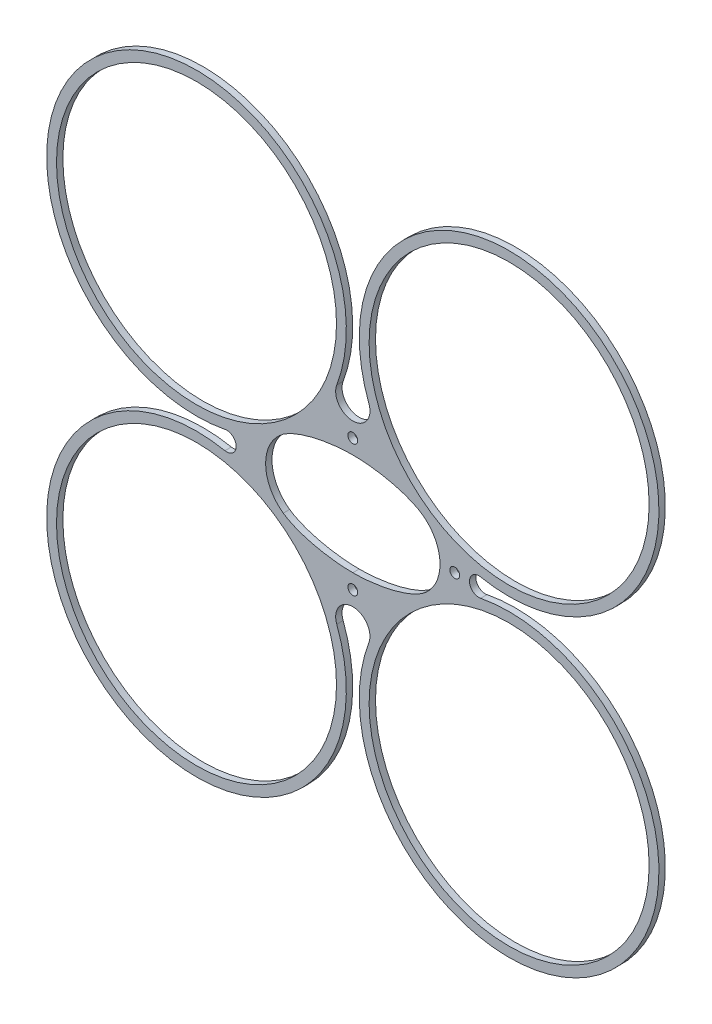
SolidWorks part; units mm, degrees
material "PC High Viscosity"
ref_plane "Front Plane" through (0, 0, 0) normal (0, 0, 1) x (1, 0, 0)
ref_plane "Top Plane" through (0, 0, 0) normal (0, 1, 0) x (1, 0, 0)
ref_plane "Right Plane" through (0, 0, 0) normal (1, 0, 0) x (0, 0, -1)
sketch "Sketch1" plane through (0, 0, 0) normal (0, 0, 1) x (1, 0, 0)
  line L0 (0, -18.1806) -> (0, 16.1577) construction
  line L1 (-47.1416, 0) -> (36.9217, 0) construction
  line L4 (-31.8198, -31.8198) -> (31.8198, 31.8198) construction
  line L6 (-31.8198, 31.8198) -> (31.8198, -31.8198) construction
  circle A0 centre (-31.8198, 31.8198) radius 28.5
  circle A2 centre (31.8198, -31.8198) radius 5.125 construction
  circle A3 centre (-31.8198, 31.8198) radius 30.5
  circle A4 centre (31.8198, 31.8198) radius 30.5
  circle A5 centre (31.8198, 31.8198) radius 28.5
  circle A6 centre (31.8198, -31.8198) radius 28.5
  circle A7 centre (31.8198, -31.8198) radius 30.5
  circle A8 centre (-31.8198, -31.8198) radius 30.5
  circle A9 centre (-31.8198, -31.8198) radius 28.5
  dimension "D1" = 57
  dimension "D2" = 2
extrude "Boss-Extrude1" add sketch "Sketch1" along normal blind 1.3
sketch "Sketch3" plane through (0, 0, 0) normal (0, 0, -1) x (-1, 0, 0)
  line L0 (-31.8198, -1.3198) -> (-31.8198, -3.3198) construction
  line L1 (-20.75, -1) -> (-20.75, -3) construction
  line L2 (-17.75, 0) -> (-23.75, 0) construction
  line L3 (-29.35, 0) -> (23.6854, 0) construction
  line L4 (0, -20.1011) -> (0, 19.2767) construction
  line L5 (0, -16.375) -> (0, -10.375) construction
  line L6 (-3, -13.375) -> (3, -13.375) construction
  line L7 (0, 0) -> (-31.8198, -31.8198) construction
  circle A0 centre (-20.75, 0) radius 1 construction
  circle A1 centre (0, 13.375) radius 1 construction
  circle A2 centre (0, -13.375) radius 1 construction
  circle A3 centre (-20.75, 0) radius 1
  circle A4 centre (0, 13.375) radius 1
  circle A5 centre (0, -13.375) radius 1
  circle A6 centre (-20.75, 0) radius 3
  circle A7 centre (-31.8198, -31.8198) radius 30.5 construction
  circle A8 centre (-31.8198, -31.8198) radius 28.5 construction
  circle A9 centre (0, -13.375) radius 3
  circle A10 centre (0, 13.375) radius 3
  arc A11 (-17.75, 0) -> (-14.1601, -6.9525) centre (-9.2227, 0) ccw
  arc A12 (-23.75, 0) -> (-26.0235, -1.8756) centre (-25.6605, 0) cw
  arc A13 (-23.75, 0) -> (-26.0235, 1.8756) centre (-25.6605, 0) ccw
  circle A14 centre (-31.8198, 31.8198) radius 30.5 construction
  arc A15 (-17.75, 0) -> (-14.1601, 6.9525) centre (-9.2227, 0) cw
  circle A16 centre (-31.8198, -31.8198) radius 30.5
  circle A17 centre (-31.8198, 31.8198) radius 30.5
  arc A18 (0, -16.375) -> (-3.2681, -21.0938) centre (0, -19.8661) ccw
  circle A19 centre (31.8198, -31.8198) radius 30.5
  circle A20 centre (31.8198, 31.8198) radius 30.5
  circle A21 centre (31.8198, 31.8198) radius 30.5 construction
  circle A22 centre (31.8198, -31.8198) radius 30.5 construction
  arc A23 (0, -16.375) -> (3.2681, -21.0938) centre (0, -19.8661) cw
  circle A24 centre (20.75, 0) radius 1
  arc A25 (0, 16.375) -> (3.2681, 21.0938) centre (0, 19.8661) ccw
  arc A26 (0, 16.375) -> (-3.2681, 21.0938) centre (0, 19.8661) cw
  arc A28 (17.75, 0) -> (14.1601, -6.9525) centre (9.2227, 0) cw
  arc A29 (17.75, 0) -> (14.1601, 6.9525) centre (9.2227, 0) ccw
  arc A30 (23.75, 0) -> (26.0235, 1.8756) centre (25.6605, 0) cw
  arc A31 (23.75, 0) -> (26.0235, -1.8756) centre (25.6605, 0) ccw
  spline S0 degree 3 poles (-14.1601, -6.9525) (-14.0064, -7.0616) (-11.2813, -8.8513) (-5.533, -10.3111) (-0.2739, -10.375) (0, -10.375) knots 0 0 0 0 0.05 0.95 1 1 1 1
  spline S1 degree 3 poles (-14.1601, 6.9525) (-14.0064, 7.0616) (-11.2813, 8.8513) (-5.533, 10.3111) (-0.2739, 10.375) (0, 10.375) knots 0 0 0 0 0.05 0.95 1 1 1 1
  spline S2 degree 3 poles (14.1601, -6.9525) (14.0064, -7.0616) (11.2813, -8.8513) (5.533, -10.3111) (0.2739, -10.375) (0, -10.375) knots 0 0 0 0 0.05 0.95 1 1 1 1
  spline S3 degree 3 poles (14.1601, 6.9525) (14.0064, 7.0616) (11.2813, 8.8513) (5.533, 10.3111) (0.2739, 10.375) (0, 10.375) knots 0 0 0 0 0.05 0.95 1 1 1 1
extrude "Boss-Extrude2" add sketch "Sketch3" against normal up to surface (1.3 mm away)
